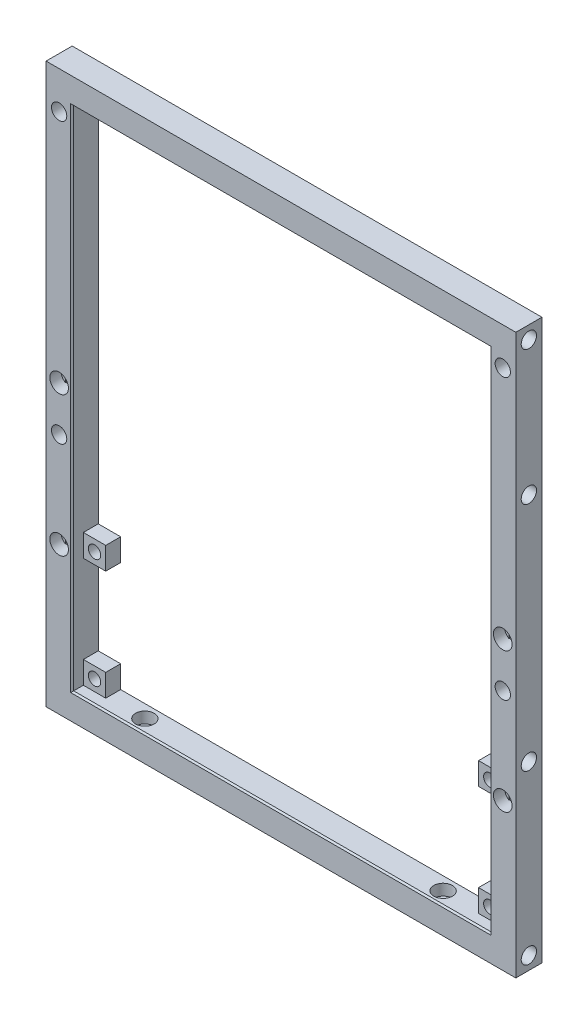
SolidWorks part; units mm, degrees
ref_plane "Front Plane" through (0, 0, 0) normal (0, 0, 1) x (1, 0, 0)
ref_plane "Top Plane" through (0, 0, 0) normal (0, 1, 0) x (1, 0, 0)
ref_plane "Right Plane" through (0, 0, 0) normal (1, 0, 0) x (0, 0, -1)
sketch "Sketch1" plane through (0, 0, 0) normal (0, 0, 1) x (1, 0, 0)
  line L1 (-63, -75) -> (63, -75)
  line L2 (-63, -75) -> (-63, 75)
  line L3 (-63, 75) -> (63, 75)
  line L4 (63, -75) -> (63, 75)
  line L5 (-63, -75) -> (63, 75) construction
  line L6 (-63, 75) -> (63, -75) construction
  line L7 (-56, -68) -> (56, -68)
  line L8 (-56, -68) -> (-56, 68)
  line L9 (-56, 68) -> (56, 68)
  line L10 (56, -68) -> (56, 68)
  line L11 (-56, -68) -> (56, 68) construction
  line L12 (-56, 68) -> (56, -68) construction
  point P0 (0, 0)
  point P6 (0, 0)
  dimension "D1" = 126
  dimension "D2" = 150
  dimension "D3" = 7
  dimension "D4" = 7
extrude "Boss-Extrude1" add sketch "Sketch1" along normal blind 7
sketch "Sketch2" plane through (63, 0, 0) normal (1, 0, 0) x (0, 0, -1)
  line L0 (-3.5, -71.5) -> (-3.5, 71.5) construction
  line L1 (-7, 75) -> (0, 75) construction
  line L3 (0, -75) -> (0, 75) construction
  circle A0 centre (-3.5, 71.5) radius 2.05
  circle A2 centre (-3.5, -71.5) radius 2.05
  circle A3 centre (-3.5, 35.5) radius 2.05
  circle A4 centre (-3.5, -26.5) radius 2.05
  point P6 (-3.5, 75)
  point P7 (-3.5, 0)
  point P14 (0, 0)
  dimension "D2" = 4.1
  dimension "D1" = 3.5
  dimension "D3" = 36
  dimension "D4" = 45
extrude "Cut-Extrude1" cut sketch "Sketch2" against normal blind 6
mirror "Mirror1" about plane through (0, 0, 0) normal (1, 0, 0) of "Cut-Extrude1"
sketch "Sketch3" plane through (0, -68, 0) normal (0, 1, 0) x (1, 0, 0)
  line L0 (0, 0) -> (0, -7) construction
  line L1 (-56, 0) -> (56, 0) construction
  line L2 (-56, -7) -> (56, -7) construction
  line L3 (-40, -3.5) -> (40, -3.5) construction
  circle A0 centre (-40, -3.5) radius 1.35
  circle A1 centre (40, -3.5) radius 1.35
  point P9 (0, -3.5)
  dimension "D2" = 2.7
  dimension "D1" = 80
extrude "Cut-Extrude2" cut sketch "Sketch3" against normal through all
sketch "Sketch4" plane through (0, -68, 0) normal (0, 1, 0) x (1, 0, 0)
  circle A0 centre (-40, -3.5) radius 2.5
  circle A1 centre (40, -3.5) radius 2.5
  dimension "D1" = 5
extrude "Cut-Extrude3" cut sketch "Sketch4" against normal blind 3
sketch "Sketch5" plane through (0, 0, 7) normal (0, 0, 1) x (1, 0, 0)
  line L0 (-56, 0) -> (-63, 0) construction
  line L1 (-56, 68) -> (-56, -68) construction
  line L2 (-63, 75) -> (-63, -75) construction
  line L3 (-59.5, -75) -> (-59.5, 75) construction
  line L4 (63, 75) -> (-63, 75) construction
  line L5 (0, 68) -> (0, -68) construction
  line L6 (56, 68) -> (-56, 68) construction
  line L7 (-56, -68) -> (56, -68) construction
  line L8 (56, 0) -> (63, 0) construction
  circle A0 centre (-59.5, 2) radius 1.35
  circle A1 centre (59.5, 2) radius 1.35
  circle A2 centre (-59.5, -35.5) radius 1.35
  circle A3 centre (59.5, -35.5) radius 1.35
  point P11 (-59.5, 0)
  point P23 (59.5, 0)
  dimension "D2" = 2.7
  dimension "D3" = 32.5
  dimension "D1" = 2
extrude "Cut-Extrude4" cut sketch "Sketch5" against normal through all
sketch "Sketch6" plane through (0, 0, 7) normal (0, 0, 1) x (1, 0, 0)
  circle A0 centre (-59.5, 2) radius 2.5
  circle A1 centre (59.5, 2) radius 2.5
  circle A2 centre (-59.5, -35.5) radius 2.5
  circle A3 centre (59.5, -35.5) radius 2.5
  dimension "D1" = 5
extrude "Cut-Extrude5" cut sketch "Sketch6" against normal blind 3
sketch "Sketch7" plane through (0, 0, 4) normal (0, 0, 1) x (1, 0, 0)
  line L2 (-60.85, -0.1042) -> (-60.85, 4.1042)
  line L4 (-58.15, -0.1042) -> (-58.15, 4.1042)
  line L5 (-60.85, -0.1042) -> (-58.15, 4.1042) construction
  line L6 (-60.85, 4.1042) -> (-58.15, -0.1042) construction
  line L8 (-60.85, -37.6042) -> (-60.85, -33.3958)
  line L10 (-58.15, -37.6042) -> (-58.15, -33.3958)
  line L11 (-60.85, -37.6042) -> (-58.15, -33.3958) construction
  line L12 (-60.85, -33.3958) -> (-58.15, -37.6042) construction
  circle A0 centre (-59.5, 2) radius 2.5 construction
  circle A1 centre (-59.5, -35.5) radius 2.5 construction
  arc A2 (-58.15, 4.1042) -> (-60.85, 4.1042) centre (-59.5, 2) ccw
  arc A3 (-60.85, -37.6042) -> (-58.15, -37.6042) centre (-59.5, -35.5) ccw
  circle A4 centre (-59.5, 2) radius 1.35 construction
  circle A5 centre (-59.5, -35.5) radius 1.35 construction
  arc A6 (-60.85, -0.1042) -> (-58.15, -0.1042) centre (-59.5, 2) ccw
  arc A7 (-58.15, -33.3958) -> (-60.85, -33.3958) centre (-59.5, -35.5) ccw
  point P0 (-59.5, 2)
  point P8 (-59.5, -35.5)
extrude "Cut-Extrude6" cut sketch "Sketch7" against normal blind 0.2
sketch "Sketch8" plane through (0, 0, 3.8) normal (0, 0, 1) x (1, 0, 0)
  line L0 (-58.15, -37.6042) -> (-58.15, -33.3958) construction
  line L1 (-60.85, -36.85) -> (-58.15, -36.85)
  line L2 (-60.85, -36.85) -> (-60.85, -34.15)
  line L3 (-60.85, -34.15) -> (-58.15, -34.15)
  line L4 (-58.15, -36.85) -> (-58.15, -34.15)
  line L5 (-60.85, -36.85) -> (-58.15, -34.15) construction
  line L6 (-60.85, -34.15) -> (-58.15, -36.85) construction
  line L7 (-58.15, -0.1042) -> (-58.15, 4.1042) construction
  line L8 (-60.85, 0.65) -> (-58.15, 0.65)
  line L9 (-60.85, 0.65) -> (-60.85, 3.35)
  line L10 (-60.85, 3.35) -> (-58.15, 3.35)
  line L11 (-58.15, 0.65) -> (-58.15, 3.35)
  line L12 (-60.85, 0.65) -> (-58.15, 3.35) construction
  line L13 (-60.85, 3.35) -> (-58.15, 0.65) construction
  arc A0 (-58.15, -35.5) -> (-60.85, -35.5) centre (-59.5, -35.5) ccw construction
  point P0 (-59.5, -35.5)
  point P11 (-59.5, 2)
extrude "Cut-Extrude7" cut sketch "Sketch8" against normal blind 0.2
mirror "Mirror2" about plane through (0, 0, 0) normal (1, 0, 0) of "Cut-Extrude6", "Cut-Extrude7"
sketch "Sketch9" plane through (0, 0, 7) normal (0, 0, 1) x (1, 0, 0)
  line L0 (-56, 68) -> (-63, 68) construction
  line L1 (-63, 75) -> (-63, -75) construction
  line L2 (-59.5, 65) -> (-59.5, -10) construction
  line L3 (63, 75) -> (-63, 75) construction
  circle A0 centre (-59.5, 65) radius 2.05
  circle A1 centre (-59.5, -10) radius 2.05
  point P8 (-59.5, 68)
  dimension "D3" = 4.1
  dimension "D1" = 10
  dimension "D2" = 75
extrude "Cut-Extrude8" cut sketch "Sketch9" against normal through all
mirror "Mirror3" about plane through (0, 0, 0) normal (1, 0, 0) of "Cut-Extrude8"
sketch "Sketch10" plane through (0, 0, 0) normal (0, 0, -1) x (-1, 0, 0)
  line L0 (56, 68) -> (56, -68) construction
  line L1 (56, -68) -> (50, -68)
  line L2 (56, -68) -> (56, -62)
  line L3 (56, -62) -> (50, -62)
  line L4 (50, -68) -> (50, -62)
  line L5 (56, -38.5) -> (50, -38.5)
  line L6 (56, -38.5) -> (56, -32.5)
  line L7 (56, -32.5) -> (50, -32.5)
  line L8 (50, -38.5) -> (50, -32.5)
  line L9 (56, -68) -> (-56, -68) construction
  dimension "D1" = 6
  dimension "D2" = 6
  dimension "D3" = 35.5
extrude "Boss-Extrude2" add sketch "Sketch10" against normal offset from surface (4 mm away) 3 up to face at (57.45, -10, 7)
sketch "Sketch11" plane through (0, 0, 4) normal (0, 0, 1) x (1, 0, 0)
  line L0 (-56, -62) -> (-50, -68) construction
  line L1 (-56, -38.5) -> (-50, -32.5) construction
  circle A0 centre (-53, -65) radius 1.65
  circle A1 centre (-53, -35.5) radius 1.65
  dimension "D1" = 3.3
extrude "Cut-Extrude9" cut sketch "Sketch11" against normal through all
mirror "Mirror4" about plane through (0, 0, 0) normal (1, 0, 0) of "Cut-Extrude9", "Boss-Extrude2"
chamfer "Chamfer1" distance 0.4 angle 45 4 edges at (0, 68, 7) (56, 0, 7) (0, -68, 7) (-56, 0, 7)
